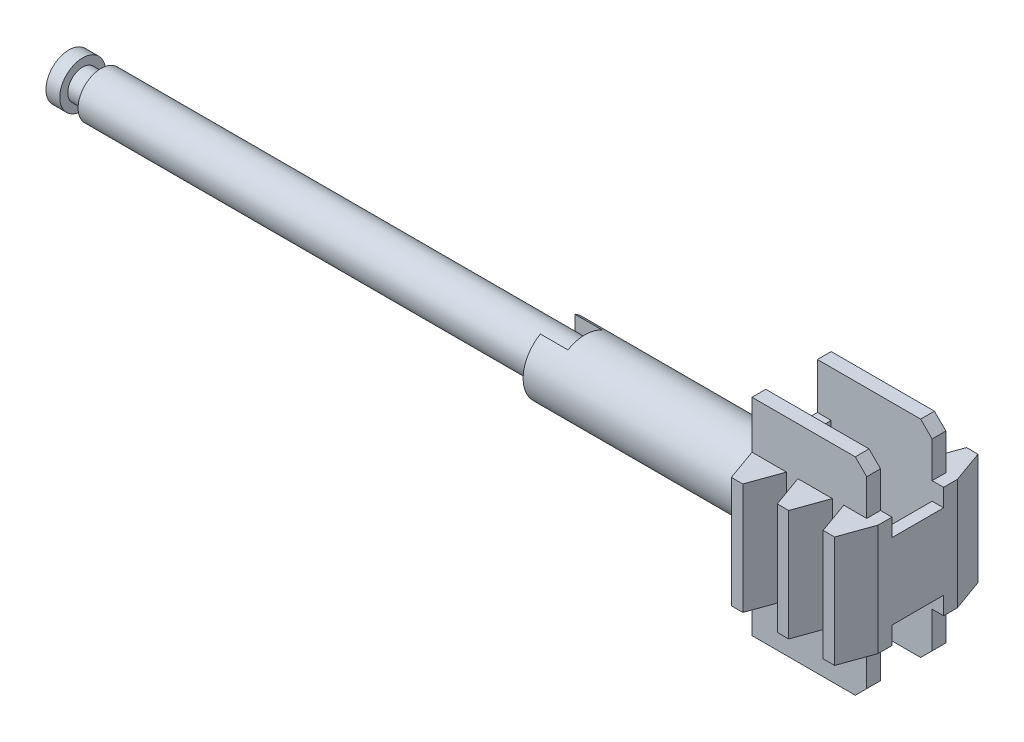
SolidWorks part; units mm, degrees
ref_plane "Front Plane" through (0, 0, 0) normal (0, 0, 1) x (1, 0, 0)
ref_plane "Top Plane" through (0, 0, 0) normal (0, 1, 0) x (1, 0, 0)
ref_plane "Right Plane" through (0, 0, 0) normal (1, 0, 0) x (0, 0, -1)
sketch "Sketch1" plane through (0, 0, 0) normal (1, 0, 0) x (0, 0, -1)
  circle A0 centre (0, 0) radius 2
  dimension "D1" = 4
extrude "Boss-Extrude1" add sketch "Sketch1" along normal blind 1.2
sketch "Sketch2" plane through (1.2, 0, 0) normal (1, 0, 0) x (0, 0, -1)
  circle A0 centre (0, 0) radius 1.3
  dimension "D1" = 2.6
extrude "Boss-Extrude2" add sketch "Sketch2" along normal blind 1.6
sketch "Sketch3" plane through (2.8, 0, 0) normal (1, 0, 0) x (0, 0, -1)
  circle A0 centre (0, 0) radius 2
  dimension "D1" = 4
extrude "Boss-Extrude3" add sketch "Sketch3" along normal blind 42.2
sketch "Sketch4" plane through (45, 0, 0) normal (1, 0, 0) x (0, 0, -1)
  circle A0 centre (0, 0) radius 3
  dimension "D1" = 6
extrude "Boss-Extrude4" add sketch "Sketch4" along normal blind 18
sketch "Sketch5" plane through (45, 0, 0) normal (-1, 0, 0) x (0, 0, 1)
  line L0 (0, 0) -> (0, 50000) construction
  line L2 (-1.5, 2.5981) -> (-1.5, -2.5981)
  line L3 (1.5, -2.5981) -> (1.5, 2.5981)
  arc A4 (-1.5, -2.5981) -> (-1.5, 2.5981) centre (0, 0) cw
  circle A5 centre (0, 0) radius 3 construction
  arc A6 (1.5, -2.5981) -> (1.5, 2.5981) centre (0, 0) ccw
  circle M5 centre (0, 0) radius 3
  dimension "D1" = 3
extrude "Boss-Extrude7" add sketch "Sketch5" along normal blind 2.4 contours L3 M5 | L2 M5
sketch "Sketch6" plane through (63, 0, 0) normal (1, 0, 0) x (0, 0, -1)
  line L1 (3.45, -5) -> (-3.45, -5)
  line L2 (3.45, -5) -> (3.45, 5)
  line L3 (3.45, 5) -> (-3.45, 5)
  line L4 (-3.45, -5) -> (-3.45, 5)
  line L5 (3.45, -5) -> (-3.45, 5) construction
  line L6 (3.45, 5) -> (-3.45, -5) construction
  point P0 (0, 0)
  dimension "D1" = 10
  dimension "D2" = 6.9
extrude "Boss-Extrude8" add sketch "Sketch6" along normal blind 1.2
sketch "Sketch7" plane through (63, 0, 0) normal (-1, 0, 0) x (0, 0, 1)
  line L0 (0, -5.5) -> (0, 5.5) construction
  line L2 (-3.45, 5) -> (-3.45, 9)
  line L3 (-3.45, 9) -> (-2.25, 9)
  line L7 (3.45, 9) -> (2.25, 9)
  line L10 (3.45, 5) -> (3.45, 9)
  line L11 (3.795, 0) -> (-3.795, 0) construction
  line L12 (3.45, -5) -> (3.45, -9)
  line L14 (2.25, 9) -> (2.25, -9)
  line L15 (3.45, -9) -> (2.25, -9)
  line L16 (-3.45, -9) -> (-2.25, -9)
  line L17 (-2.25, 9) -> (-2.25, -9)
  line L19 (-3.45, -5) -> (-3.45, -9)
  line L20 (-3.45, 5) -> (-3.45, -5)
  line L23 (3.45, -5) -> (3.45, 5)
  point P3 (0, 0)
  point P4 (-2.85, 7)
  point P10 (0, 0)
  point P22 (0, 0)
  point P23 (0, 0)
  dimension "D1" = 1.2
  dimension "D2" = 4
extrude "Boss-Extrude9" add sketch "Sketch7" against normal blind 10
chamfer "Chamfer1" distance 1 angle 45 4 edges at (73, -9, 2.85) (73, -9, -2.85) (73, 9, 2.85) (73, 9, -2.85)
sketch "Sketch8" plane through (0, 0, 0) normal (0, 1, 0) x (1, 0, 0)
  line L0 (63, 3.45) -> (66, 3.45)
  line L1 (72, 3.45) -> (63, 3.45) construction
  line L2 (63, 3.45) -> (64, 6.25)
  line L3 (66, 3.45) -> (65, 6.25)
  line L4 (64, 6.25) -> (65, 6.25)
  line L5 (68, 6.25) -> (69, 6.25)
  line L6 (70, 3.45) -> (69, 6.25)
  line L7 (67, 3.45) -> (70, 3.45)
  line L8 (67, 3.45) -> (68, 6.25)
  line L9 (72, 6.25) -> (73, 6.25)
  line L10 (74, 3.45) -> (73, 6.25)
  line L11 (71, 3.45) -> (74, 3.45)
  line L12 (71, 3.45) -> (72, 6.25)
  dimension "D1" = 3
  dimension "D2" = 2.8
  dimension "D3" = 1
  dimension "D4" = 3
extrude "Boss-Extrude10" add sketch "Sketch8" along normal mid plane 9.7
mirror "Mirror1" about plane through (0, 0, 0) normal (0, 0, 1) of "Boss-Extrude10"
sketch "Sketch9" plane through (73, 0, 0) normal (1, 0, 0) x (0, 0, -1)
  line L1 (3.45, 4.85) -> (-3.45, 4.85)
  line L2 (3.45, 4.85) -> (3.45, -4.85)
  line L3 (3.45, -4.85) -> (-3.45, -4.85)
  line L4 (-3.45, 4.85) -> (-3.45, -4.85)
  line L5 (3.45, 4.85) -> (-3.45, -4.85) construction
  line L6 (3.45, -4.85) -> (-3.45, 4.85) construction
  point P4 (0, 0)
extrude "Boss-Extrude11" add sketch "Sketch9" along normal blind 1
sketch "Sketch11" plane through (74, 0, 0) normal (1, 0, 0) x (0, 0, -1)
  line L0 (-2.25, -4.85) -> (-2.25, -8) construction
  line L1 (2.25, 3.3) -> (-2.25, 3.3) construction
  line L2 (2.25, 3.3) -> (2.25, -3.3) construction
  line L3 (2.25, -3.3) -> (-2.25, -3.3) construction
  line L4 (-2.25, 3.3) -> (-2.25, -3.3) construction
  line L5 (2.25, 3.3) -> (-2.25, -3.3) construction
  line L6 (2.25, -3.3) -> (-2.25, 3.3) construction
  line L7 (2.25, 5) -> (2.25, -5) construction
  line L8 (-2.25, -3.3) -> (2.25, -3.3)
  line L9 (-2.25, -3.3) -> (-2.25, -4.85)
  line L10 (-2.25, -4.85) -> (2.25, -4.85)
  line L11 (2.25, -3.3) -> (2.25, -4.85)
  line L12 (-2.25, -3.3) -> (2.25, -4.85) construction
  line L13 (-2.25, -4.85) -> (2.25, -3.3) construction
  line L14 (-3.45, -4.85) -> (3.45, -4.85) construction
  line L16 (2.25, 3.3) -> (-2.25, 3.3)
  line L17 (2.25, 3.3) -> (2.25, 4.85)
  line L18 (2.25, 4.85) -> (-2.25, 4.85)
  line L19 (-2.25, 3.3) -> (-2.25, 4.85)
  line L20 (2.25, 3.3) -> (-2.25, 4.85) construction
  line L21 (2.25, 4.85) -> (-2.25, 3.3) construction
  point P0 (0, 0)
  point P10 (0, -4.075)
  point P17 (0, 4.075)
  line M6 (3.45, 4.85) -> (-3.45, 4.85)
  line M8 (-3.45, -4.85) -> (3.45, -4.85)
  dimension "D1" = 6.6
extrude "Cut-Extrude1" cut sketch "Sketch11" against normal up to surface (1 mm away) contours L11 L8 L9 M8 | L19 L16 L17 M6 up to face at (73, 0, 0)
